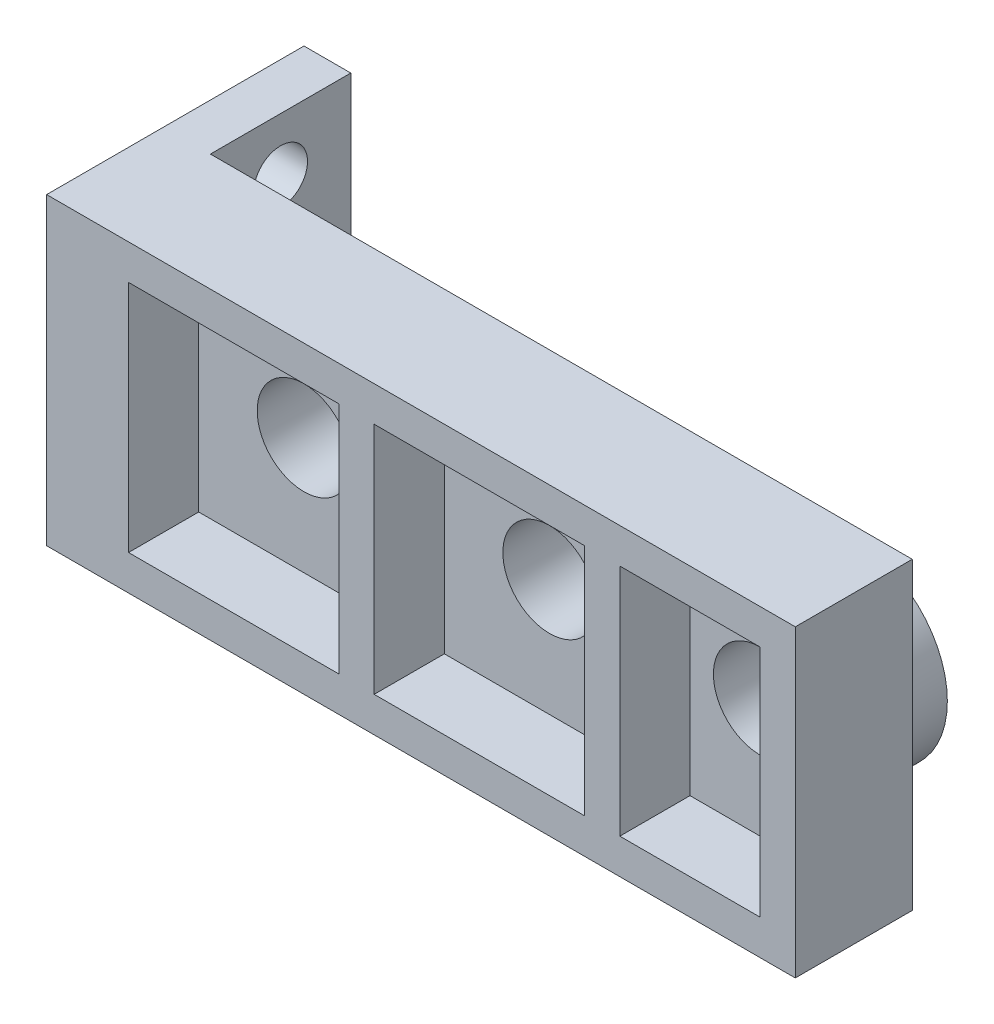
SolidWorks part; units mm, degrees
ref_plane "Front Plane" through (0, 0, 0) normal (0, 0, 1) x (1, 0, 0)
ref_plane "Top Plane" through (0, 0, 0) normal (0, 1, 0) x (1, 0, 0)
ref_plane "Right Plane" through (0, 0, 0) normal (1, 0, 0) x (0, 0, -1)
sketch "Sketch1" plane through (0, 0, 0) normal (0, 0, 1) x (1, 0, 0)
  line L1 (-15, 6.5) -> (15, 6.5)
  line L2 (-15, 6.5) -> (-15, -6.5)
  line L3 (-15, -6.5) -> (15, -6.5)
  line L4 (15, 6.5) -> (15, -6.5)
  line L5 (-15, 6.5) -> (15, -6.5) construction
  line L6 (-15, -6.5) -> (15, 6.5) construction
  point P0 (0, 0)
  dimension "D1" = 13
  dimension "D2" = 30
extrude "Boss-Extrude1" add sketch "Sketch1" along normal blind 5
sketch "Sketch2" plane through (0, 0, 5) normal (0, 0, 1) x (1, 0, 0)
  line L0 (15, 6.5) -> (-15, 6.5) construction
  line L1 (-13.5, 5) -> (-4.5, 5)
  line L2 (-13.5, 5) -> (-13.5, -5)
  line L3 (-13.5, -5) -> (-4.5, -5)
  line L4 (-4.5, 5) -> (-4.5, -5)
  line L5 (-3, 5) -> (6, 5)
  line L6 (-3, 5) -> (-3, -5)
  line L7 (-3, -5) -> (6, -5)
  line L8 (6, 5) -> (6, -5)
  line L9 (7.5, 5) -> (13.5, 5)
  line L10 (7.5, 5) -> (7.5, -5)
  line L11 (7.5, -5) -> (13.5, -5)
  line L12 (13.5, 5) -> (13.5, -5)
  line L13 (-15, 6.5) -> (-15, -6.5) construction
  line L14 (-15, -6.5) -> (15, -6.5) construction
  line L15 (15, -6.5) -> (15, 6.5) construction
  dimension "D1" = 1.5
  dimension "D2" = 1.5
  dimension "D3" = 1.5
  dimension "D4" = 1.5
  dimension "D5" = 1.5
  dimension "D6" = 1.5
  dimension "D7" = 1.5
  dimension "D8" = 1.5
  dimension "D9" = 1.5
  dimension "D10" = 1.5
  dimension "D11" = 9
  dimension "D12" = 9
extrude "Cut-Extrude1" cut sketch "Sketch2" against normal blind 3
sketch "Sketch3" plane through (0, 0, 2) normal (0, 0, 1) x (1, 0, 0)
  line L0 (-9, 5) -> (-9, -5) construction
  line L1 (-4.5, 5) -> (-13.5, 5) construction
  line L2 (-13.5, -5) -> (-4.5, -5) construction
  line L3 (-13.5, 0) -> (15, 0) construction
  line L4 (-13.5, 5) -> (-13.5, -5) construction
  line L5 (15, -6.5) -> (15, 6.5) construction
  line L6 (1.5, 5) -> (1.5, -5) construction
  line L7 (6, 5) -> (-3, 5) construction
  line L8 (-3, -5) -> (6, -5) construction
  line L9 (10.5, 5) -> (10.5, -5) construction
  line L10 (13.5, 5) -> (7.5, 5) construction
  line L11 (7.5, -5) -> (13.5, -5) construction
  circle A0 centre (-9, 0) radius 2
  circle A1 centre (1.5, 0) radius 2
  circle A2 centre (10.5, 0) radius 2
  dimension "D1" = 3.7
  dimension "D2" = 3.7
  dimension "D3" = 3.7
extrude "Cut-Extrude2" cut sketch "Sketch3" against normal blind 5
sketch "Sketch4" plane through (-15, 0, 0) normal (-1, 0, 0) x (0, 0, 1)
  line L1 (5, 6.5) -> (-6, 6.5)
  line L2 (5, 6.5) -> (5, -6.5)
  line L3 (5, -6.5) -> (-6, -6.5)
  line L4 (-6, 6.5) -> (-6, -6.5)
  dimension "D1" = 11
extrude "Boss-Extrude2" add sketch "Sketch4" along normal blind 2
sketch "Sketch5" plane through (-15, 0, 0) normal (1, 0, 0) x (0, 0, -1)
  line L0 (3, 6.5) -> (3, -6.5) construction
  line L1 (0, 6.5) -> (6, 6.5) construction
  line L2 (6, -6.5) -> (0, -6.5) construction
  circle A0 centre (3, 4.1582) radius 1.15
  circle A1 centre (3, -2.5791) radius 1.15
  dimension "D1" = 2.3
  dimension "D2" = 2.3
extrude "Cut-Extrude3" cut sketch "Sketch5" against normal blind 2
sketch "Sketch6" plane through (0, 0, 0) normal (0, 0, -1) x (-1, 0, 0)
  circle A0 centre (9, 0) radius 2 construction
  circle A1 centre (-1.5, 0) radius 2 construction
  circle A2 centre (-10.5, 0) radius 2 construction
  circle A3 centre (9, 0) radius 2
  circle A4 centre (-1.5, 0) radius 2
  circle A5 centre (-10.5, 0) radius 2
  circle A6 centre (-10.5, 0) radius 4
  circle A7 centre (-1.5, 0) radius 4
  circle A8 centre (9, 0) radius 4
  dimension "D1" = 2
extrude "Boss-Extrude3" add sketch "Sketch6" along normal blind 2
